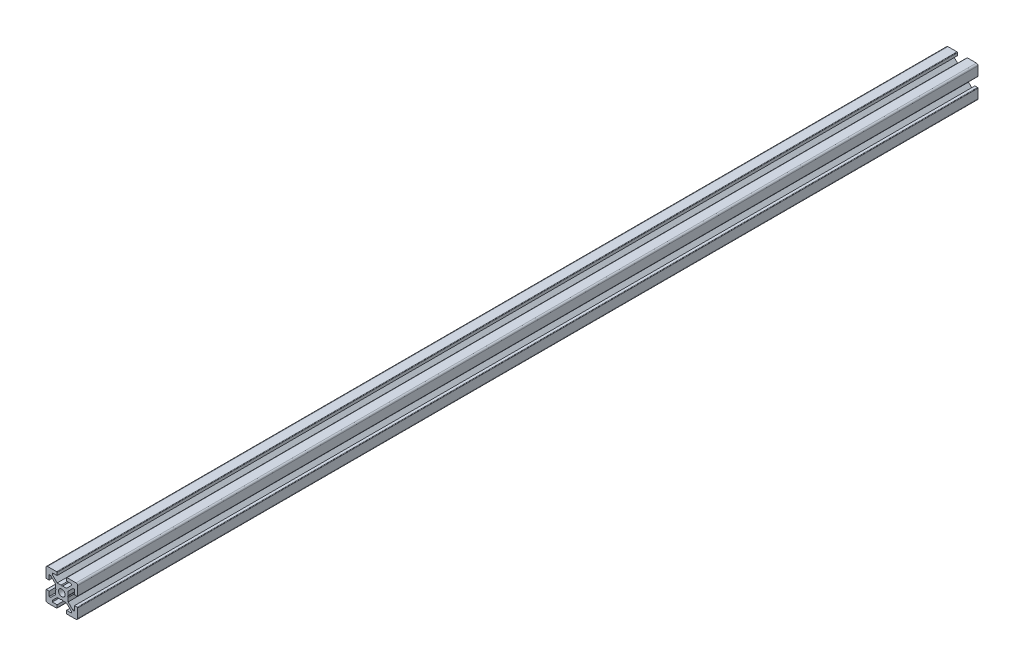
SolidWorks part; units mm, degrees
material "6063-T5"
ref_plane "Front Plane" through (0, 0, 0) normal (0, 0, 1) x (1, 0, 0)
ref_plane "Top Plane" through (0, 0, 0) normal (0, 1, 0) x (1, 0, 0)
ref_plane "Right Plane" through (0, 0, 0) normal (1, 0, 0) x (0, 0, -1)
ref_plane "Plane1" through (0, 0, 0) normal (0, 0, 1) x (1, 0, 0)
sketch "Sketch1" plane through (0, 0, 0) normal (0, 0, 1) x (1, 0, 0)
  line L0 (-10, 9) -> (-10, 3.3)
  line L1 (-9.7, 3) -> (-8, 3)
  line L2 (-8, 3) -> (-8, 6)
  line L3 (-8, 6) -> (-7.0607, 6)
  line L4 (-7.0607, 6) -> (-4, 2.9393)
  line L5 (-4, 2.9393) -> (-4, 0.5196)
  line L6 (-4, 0.5196) -> (-3.7, 0)
  line L7 (-3.7, 0) -> (-4, -0.5196)
  line L8 (-4, -0.5196) -> (-4, -2.9393)
  line L9 (-4, -2.9393) -> (-7.0607, -6)
  line L10 (-7.0607, -6) -> (-8, -6)
  line L11 (-8, -6) -> (-8, -3)
  line L12 (-8, -3) -> (-9.7, -3)
  line L13 (-10, -3.3) -> (-10, -9)
  line L14 (-9, -10) -> (-3.3, -10)
  line L15 (-3, -9.7) -> (-3, -8)
  line L16 (-3, -8) -> (-6, -8)
  line L17 (-6, -8) -> (-6, -7.0607)
  line L18 (-6, -7.0607) -> (-2.9393, -4)
  line L19 (-2.9393, -4) -> (-0.5196, -4)
  line L20 (-0.5196, -4) -> (0, -3.7)
  line L21 (0, -3.7) -> (0.5196, -4)
  line L22 (0.5196, -4) -> (2.9393, -4)
  line L23 (2.9393, -4) -> (6, -7.0607)
  line L24 (6, -7.0607) -> (6, -8)
  line L25 (6, -8) -> (3, -8)
  line L26 (3, -8) -> (3, -9.7)
  line L27 (3.3, -10) -> (9, -10)
  line L28 (10, -9) -> (10, -3.3)
  line L29 (9.7, -3) -> (8, -3)
  line L30 (8, -3) -> (8, -6)
  line L31 (8, -6) -> (7.0606, -6)
  line L32 (7.0606, -6) -> (4, -2.9393)
  line L33 (4, -2.9393) -> (4, -0.5196)
  line L34 (4, -0.5196) -> (3.7, 0)
  line L35 (3.7, 0) -> (4, 0.5196)
  line L36 (4, 0.5196) -> (4, 2.9393)
  line L37 (4, 2.9393) -> (7.0607, 6)
  line L38 (7.0607, 6) -> (8, 6)
  line L39 (8, 6) -> (8, 3)
  line L40 (8, 3) -> (9.7, 3)
  line L41 (10, 3.3) -> (10, 9)
  line L42 (9, 10) -> (3.3, 10)
  line L43 (3, 9.7) -> (3, 8)
  line L44 (3, 8) -> (6, 8)
  line L45 (6, 8) -> (6, 7.0607)
  line L46 (6, 7.0607) -> (2.9393, 4)
  line L47 (2.9393, 4) -> (0.5196, 4)
  line L48 (0.5196, 4) -> (0, 3.7)
  line L49 (0, 3.7) -> (-0.5196, 4)
  line L50 (-0.5196, 4) -> (-2.9394, 4)
  line L51 (-2.9394, 4) -> (-6, 7.0606)
  line L52 (-6, 7.0606) -> (-6, 8)
  line L53 (-6, 8) -> (-3, 8)
  line L54 (-3, 8) -> (-3, 9.7)
  line L55 (-3.3, 10) -> (-9, 10)
  arc A0 (-10, 3.3) -> (-9.7, 3) centre (-9.7, 3.3) ccw
  arc A1 (-9.7, -3) -> (-10, -3.3) centre (-9.7, -3.3) ccw
  arc A2 (-10, -9) -> (-9, -10) centre (-9, -9) ccw
  arc A3 (-3.3, -10) -> (-3, -9.7) centre (-3.3, -9.7) ccw
  arc A4 (3, -9.7) -> (3.3, -10) centre (3.3, -9.7) ccw
  arc A5 (9, -10) -> (10, -9) centre (9, -9) ccw
  arc A6 (10, -3.3) -> (9.7, -3) centre (9.7, -3.3) ccw
  arc A7 (9.7, 3) -> (10, 3.3) centre (9.7, 3.3) ccw
  arc A8 (10, 9) -> (9, 10) centre (9, 9) ccw
  arc A9 (3.3, 10) -> (3, 9.7) centre (3.3, 9.7) ccw
  arc A10 (-3, 9.7) -> (-3.3, 10) centre (-3.3, 9.7) ccw
  arc A11 (-9, 10) -> (-10, 9) centre (-9, 9) ccw
extrude "Boss-Extrude1" add sketch "Sketch1" against normal blind 569.5
ref_plane "Plane2" through (0, 0, 0) normal (1, 0, 0) x (0, 0, -1)
sketch "Sketch2" plane through (0, 0, 0) normal (1, 0, 0) x (0, 0, -1)
  line L0 (0, 0) -> (0, 2.1)
  line L1 (0, 2.1) -> (609.5, 2.1)
  line L2 (609.5, 2.1) -> (609.5, 0)
  line L3 (609.5, 0) -> (0, 0)
  line L4 (609.5, 0) -> (0, 0) construction
revolve "Cut-Revolve1" cut sketch "Sketch2" angle 360 about L4
sketch "Sketch3" plane through (10, 0, 0) normal (1, 0, 0) x (0, 0, -1)
  line L0 (569.5, 0) -> (0, 0) construction
  circle A0 centre (284.75, 0) radius 2.5
  dimension "D1" = 5
extrude "Cut-Extrude1" cut sketch "Sketch3" against normal up to surface (20 mm away) up to face at (-10, 6.15, -284.75)
